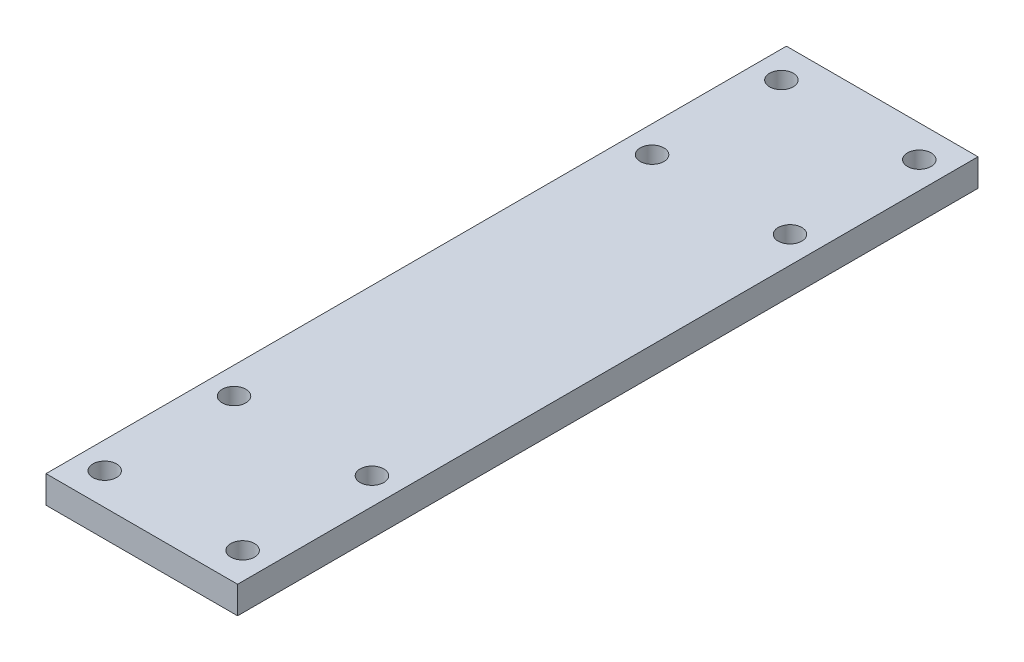
SolidWorks part; units mm, degrees
ref_plane "Front Plane" through (0, 0, 0) normal (0, 0, 1) x (1, 0, 0)
ref_plane "Top Plane" through (0, 0, 0) normal (0, 1, 0) x (1, 0, 0)
ref_plane "Right Plane" through (0, 0, 0) normal (1, 0, 0) x (0, 0, -1)
sketch "Sketch1" plane through (0, 0, 0) normal (0, 1, 0) x (1, 0, 0)
  line L1 (-22.225, -85.895) -> (22.225, -85.895)
  line L2 (-22.225, -85.895) -> (-22.225, 85.895)
  line L3 (-22.225, 85.895) -> (22.225, 85.895)
  line L4 (22.225, -85.895) -> (22.225, 85.895)
  line L5 (-22.225, -85.895) -> (22.225, 85.895) construction
  line L6 (-22.225, 85.895) -> (22.225, -85.895) construction
  point P0 (0, 0)
  dimension "D1" = 171.79
  dimension "D2" = 44.45
extrude "Boss-Extrude1" add sketch "Sketch1" along normal blind 6.35
hole_wizard "M5 Clearance Hole1" positions "Sketch2" profile "Sketch3" hole size "M5" standard "ANSI Metric" end condition through all
sketch "Sketch2" plane through (0, 6.35, 0) normal (0, 1, 0) x (1, 0, 0)
  circle A0 centre (16, -48.5) radius 2.1 construction
  circle A1 centre (16, -78.5) radius 2.1 construction
  circle A2 centre (-16, -78.5) radius 2.1 construction
  circle A3 centre (-16, -48.5) radius 2.1 construction
  circle A4 centre (-16, 48.5) radius 2.1 construction
  circle A5 centre (-16, 78.5) radius 2.1 construction
  circle A6 centre (16, 78.5) radius 2.1 construction
  circle A7 centre (16, 48.5) radius 2.1 construction
  circle A8 centre (16, -48.5) radius 2.1 construction
  circle A9 centre (16, -78.5) radius 2.1 construction
  circle A10 centre (-16, -78.5) radius 2.1 construction
  circle A11 centre (-16, -48.5) radius 2.1 construction
  circle A12 centre (-16, 48.5) radius 2.1 construction
  circle A13 centre (-16, 78.5) radius 2.1 construction
  circle A14 centre (16, 78.5) radius 2.1 construction
  circle A15 centre (16, 48.5) radius 2.1 construction
  point P29 (16, 78.5)
  point P32 (16, 48.5)
  point P35 (-16, 78.5)
  point P38 (-16, 48.5)
  point P41 (16, -48.5)
  point P44 (16, -78.5)
  point P47 (-16, -78.5)
  point P50 (-16, -48.5)
sketch "Sketch3" plane through (-16, 6.35, 48.5) normal (1, 0, 0) x (0, 0, 1)
  line L0 (0, 0) -> (0, 6.35)
  line L1 (0, 6.35) -> (2.75, 6.35)
  line L2 (2.75, 6.35) -> (2.75, 0)
  line L5 (2.75, 0) -> (0, 0)
  line L11 (0, -6.35) -> (0, 107.95) construction
  dimension "Thru Hole Dia." = 5.5
  dimension "Thru Hole Depth" = 6.35
equation "\"length\"= 9.75in - ( 37.93mm * 2 )"
equation "\"width\"= 1.75in"
equation "\"thick\"= .25in"
equation "\"D1@Boss-Extrude1\"= \"thick\""
equation "\"D1@Sketch1\"=\"length\""
equation "\"D2@Sketch1\"=\"width\""
